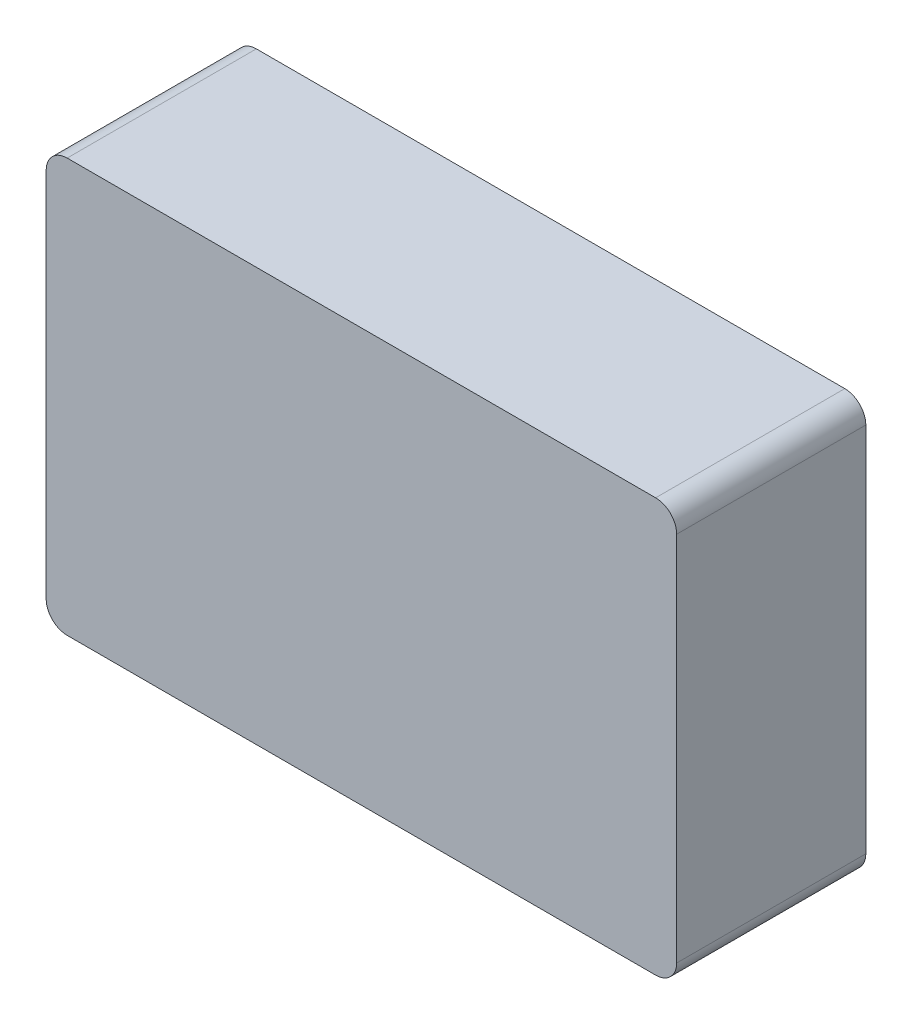
SolidWorks part; units mm, degrees
ref_plane "Front Plane" through (0, 0, 0) normal (0, 0, 1) x (1, 0, 0)
ref_plane "Top Plane" through (0, 0, 0) normal (0, 1, 0) x (1, 0, 0)
ref_plane "Right Plane" through (0, 0, 0) normal (1, 0, 0) x (0, 0, -1)
sketch "Sketch2" plane through (0, 0, 0) normal (0, 0, 1) x (1, 0, 0)
  line L1 (-14, -9.835) -> (14, -9.835)
  line L2 (-15, -8.835) -> (-15, 8.835)
  line L3 (-14, 9.835) -> (14, 9.835)
  line L4 (15, -8.835) -> (15, 8.835)
  line L5 (-15, -9.835) -> (15, 9.835) construction
  line L6 (-15, 9.835) -> (15, -9.835) construction
  arc A0 (-14, -9.835) -> (-15, -8.835) centre (-14, -8.835) cw
  arc A1 (14, -9.835) -> (15, -8.835) centre (14, -8.835) ccw
  arc A2 (14, 9.835) -> (15, 8.835) centre (14, 8.835) cw
  arc A3 (-15, 8.835) -> (-14, 9.835) centre (-14, 8.835) cw
  point P0 (0, 0)
  dimension "D3" = 1
  dimension "D1" = 30
  dimension "D2" = 19.6699
extrude "Boss-Extrude1" add sketch "Sketch2" along normal blind 9
